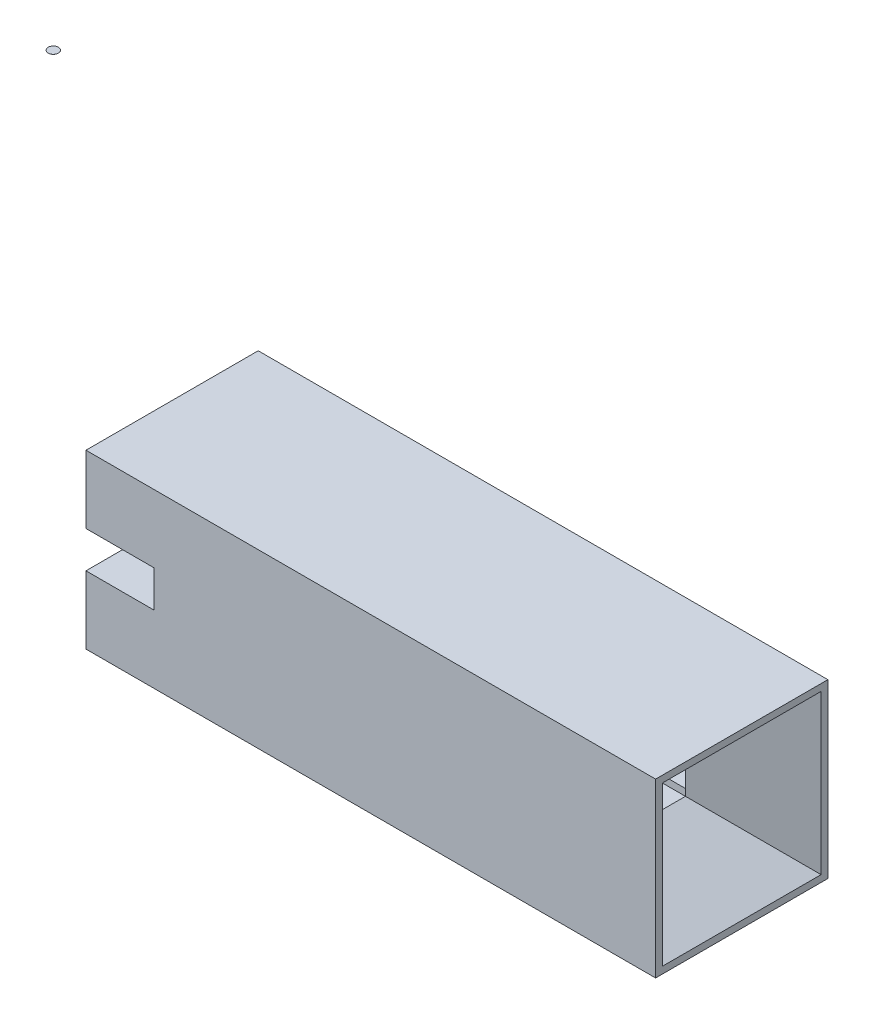
SolidWorks part; units mm, degrees
material "ABS PC"
ref_plane "Front Plane" through (0, 0, 0) normal (0, 0, 1) x (1, 0, 0)
ref_plane "Top Plane" through (0, 0, 0) normal (0, 1, 0) x (1, 0, 0)
ref_plane "Right Plane" through (0, 0, 0) normal (1, 0, 0) x (0, 0, -1)
sketch "Sketch1" plane through (0, 0, 0) normal (0, 0, 1) x (1, 0, 0)
  line L1 (0, 0) -> (8.4, 0)
  line L2 (0, 0) -> (0, 2.54)
  line L3 (0, 2.54) -> (8.4, 2.54)
  line L4 (8.4, 0) -> (8.4, 2.54)
  dimension "D1" = 2.54
  dimension "D2" = 8.4
extrude "Boss-Extrude1" add sketch "Sketch1" along normal blind 2.54
sketch "Sketch2" plane through (8.4, 0, 0) normal (1, 0, 0) x (0, 0, -1)
  line L0 (-2.54, 2.54) -> (0, 2.54) construction
  line L1 (-1.64, 1.64) -> (-0.9, 1.64)
  line L2 (-1.64, 1.64) -> (-1.64, 0.9)
  line L3 (-1.64, 0.9) -> (-0.9, 0.9)
  line L4 (-0.9, 1.64) -> (-0.9, 0.9)
  line L5 (-2.54, 0) -> (0, 0) construction
  line L6 (-2.54, 0) -> (-2.54, 2.54) construction
  dimension "D1" = 0.9
  dimension "D2" = 0.9
  dimension "D3" = 0.9
  dimension "D4" = 0.74
extrude "Cut-Extrude1" cut sketch "Sketch2" against normal up to next
chamfer "Chamfer2" distance 0.8 distance2 1.2 4 edges at (8.4, 1.27, 1.64) (8.4, 0.9, 1.27) (8.4, 1.27, 0.9) (8.4, 1.64, 1.27)
sketch "Sketch3" plane through (0, 0, 0) normal (-1, 0, 0) x (0, 0, 1)
  line L0 (0, 2.54) -> (0, 0) construction
  line L1 (0, 1.54) -> (2.54, 1.54)
  line L2 (0, 1.54) -> (0, 1)
  line L3 (0, 1) -> (2.54, 1)
  line L4 (2.54, 1.54) -> (2.54, 1)
  line L5 (2.54, 2.54) -> (2.54, 0) construction
  line L6 (2.54, 0) -> (0, 0) construction
  line L7 (2.54, 2.54) -> (0, 2.54) construction
  dimension "D1" = 1
  dimension "D2" = 1
extrude "Cut-Extrude2" cut sketch "Sketch3" against normal blind 1
sketch "Sketch5" plane through (1, 0, 0) normal (-1, 0, 0) x (0, 0, 1)
  line L0 (1.64, 1) -> (2.54, 1) construction
  line L1 (2.14, 1) -> (0.4, 1)
  line L2 (2.14, 1) -> (2.14, 1.54)
  line L3 (2.14, 1.54) -> (0.4, 1.54)
  line L4 (0.4, 1) -> (0.4, 1.54)
  line L5 (0.9, 1.54) -> (0, 1.54) construction
  line L6 (0, 1.54) -> (0, 1) construction
  line L7 (2.54, 1) -> (2.54, 1.54) construction
  dimension "D1" = 0.4
  dimension "D2" = 0.4
extrude "Cut-Extrude4" cut sketch "Sketch5" against normal up to vertex (4.34 mm away)
sketch "Skizze1" plane through (0, 2.54, 0) normal (0, 1, 0) x (1, 0, 0)
  line L0 (-1.8513, -1.195) -> (-1.6513, -1.345) construction
  line L2 (-1.6513, -1.195) -> (-1.8513, -1.195) construction
  circle A0 centre (-1.7513, -1.27) radius 0.075
extrude "Aufsatz-Linear austragen1" add sketch "Skizze1" along normal blind 0.001 from surface at 3.597 separate body
